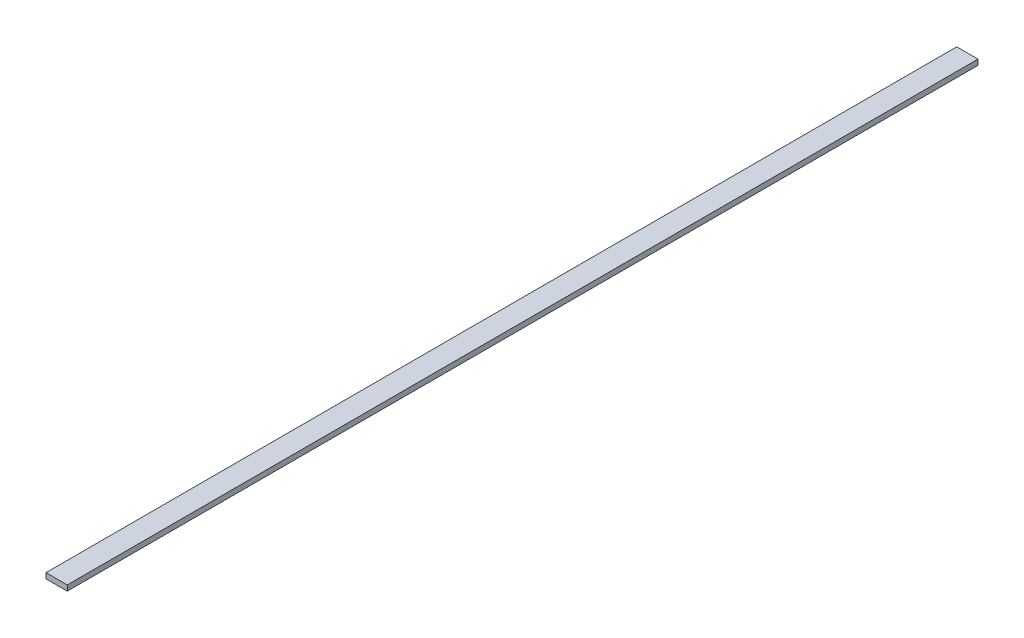
SolidWorks part; units mm, degrees
ref_plane "Front Plane" through (0, 0, 0) normal (0, 0, 1) x (1, 0, 0)
ref_plane "Top Plane" through (0, 0, 0) normal (0, 1, 0) x (1, 0, 0)
ref_plane "Right Plane" through (0, 0, 0) normal (1, 0, 0) x (0, 0, -1)
sketch "Sketch1" plane through (0, 0, 0) normal (0, 0, 1) x (1, 0, 0)
  line L1 (0, 0) -> (21.6, 0)
  line L2 (0, 0) -> (0, 5.5)
  line L3 (0, 5.5) -> (21.6, 5.5)
  line L4 (21.6, 0) -> (21.6, 5.5)
  dimension "D1" = 21.6
  dimension "D2" = 5.5
extrude "Boss-Extrude1" add sketch "Sketch1" along normal blind 925
equation "\"SlotWidth\"= 22mm"
equation "\"D1@Sketch1\"= \"SpacerWidth\""
equation "\"SpacerHeight\" = 5.5mm"
equation "\"D2@Sketch1\"= \"SpacerHeight\""
equation "\"AxialLength\"= 925mm"
equation "\"D1@Boss-Extrude1\"= \"AxialLength\""
equation "\"CarbonPaperThickness\"= 0.2mm"
equation "\"SpacerWidth\"= \"SlotWidth\" - \"CarbonPaperThickness\" * 2"
